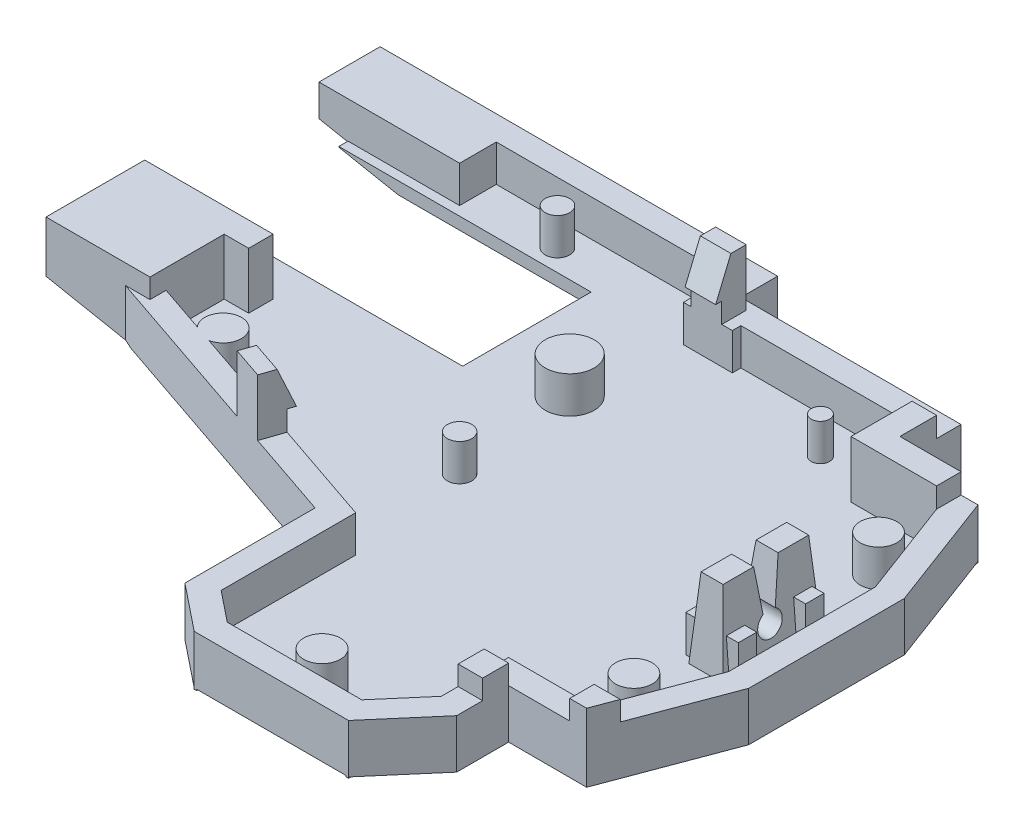
SolidWorks part; units mm, degrees
ref_plane "Front Plane" through (0, 0, 0) normal (0, 0, 1) x (1, 0, 0)
ref_plane "Top Plane" through (0, 0, 0) normal (0, 1, 0) x (1, 0, 0)
ref_plane "Right Plane" through (0, 0, 0) normal (1, 0, 0) x (0, 0, -1)
sketch "Sketch13" plane through (0, 0, 0) normal (0, 1, 0) x (1, 0, 0)
  line L1 (0, 0) -> (50, 0)
  line L2 (0, 0) -> (0, -45)
  line L3 (0, -45) -> (50, -45)
  line L4 (50, 0) -> (50, -45)
  dimension "D1" = 50
extrude "Boss-Extrude4" add sketch "Sketch13" along normal blind 1.6
sketch "Sketch14" plane through (0, 1.6, 0) normal (0, 1, 0) x (1, 0, 0)
  line L1 (50, 0) -> (40, 0)
  line L2 (50, 0) -> (50, -8)
  line L3 (50, -8) -> (40, -8)
  line L4 (40, 0) -> (40, -8)
extrude "Cut-Extrude6" cut sketch "Sketch14" against normal through all
sketch "Sketch15" plane through (0, 1.6, 0) normal (0, 1, 0) x (1, 0, 0)
  line L1 (40, 0) -> (22, 0)
  line L2 (40, 0) -> (40, -3)
  line L3 (40, -3) -> (22, -3)
  line L4 (22, 0) -> (22, -3)
extrude "Cut-Extrude7" cut sketch "Sketch15" against normal through all
sketch "Sketch16" plane through (0, 1.6, 0) normal (0, 1, 0) x (1, 0, 0)
  line L1 (22, -3) -> (26, -3)
  line L2 (22, -3) -> (22, -3.7)
  line L3 (22, -3.7) -> (26, -3.7)
  line L4 (26, -3) -> (26, -3.7)
  dimension "D1" = 0.7
  dimension "D2" = 4
extrude "Cut-Extrude8" cut sketch "Sketch16" against normal through all
sketch "Sketch17" plane through (0, 1.6, 0) normal (0, 1, 0) x (1, 0, 0)
  line L3 (40, -8) -> (50, -8) construction
  line L4 (47, -8) -> (50, -16)
  line L6 (50, -45) -> (50, -8) construction
  line L7 (50, -16) -> (65.8811, -16)
  line L8 (65.8811, -16) -> (65.8811, 17.9573)
  line L9 (65.8811, 17.9573) -> (47, 17.9573)
  line L10 (47, 17.9573) -> (47, -8)
extrude "Cut-Extrude9" cut sketch "Sketch17" against normal through all
sketch "Sketch18" plane through (0, 1.6, 0) normal (0, 1, 0) x (1, 0, 0)
  line L0 (40, -8) -> (40, -36) construction
  line L2 (40, -36) -> (61.1096, -36)
  line L3 (40, -36) -> (40, -58.8405)
  line L4 (40, -58.8405) -> (61.1096, -58.8405)
  line L5 (61.1096, -36) -> (61.1096, -58.8405)
extrude "Cut-Extrude10" cut sketch "Sketch18" against normal through all
sketch "Sketch21" plane through (0, 1.6, 0) normal (0, 1, 0) x (1, 0, 0)
  line L0 (50, -16) -> (27.9365, -16) construction
  line L1 (47, -36) -> (47, -28) construction
  line L2 (50, -36) -> (40, -36) construction
  line L3 (50, -28) -> (47, -36)
  line L4 (50, -36) -> (50, -16) construction
  line L5 (47, -36) -> (47, -49.2976)
  line L6 (47, -49.2976) -> (75.1968, -49.2976)
  line L7 (75.1968, -49.2976) -> (75.1968, -28)
  line L8 (75.1968, -28) -> (50, -28)
extrude "Cut-Extrude11" cut sketch "Sketch21" against normal through all
sketch "Sketch22" plane through (0, 1.6, 0) normal (0, 1, 0) x (1, 0, 0)
  line L0 (0, 0) -> (0, -19.3362) construction
  line L1 (0, 0) -> (0, -45) construction
  line L4 (0, -19.3362) -> (2, -19.3362)
  line L5 (0, -19.3362) -> (0, -22.3362)
  line L6 (0, -22.3362) -> (2, -22.3362)
  line L7 (2, -19.3362) -> (2, -22.3362)
  dimension "D1" = 2
  dimension "D2" = 3
extrude "Cut-Extrude12" cut sketch "Sketch22" against normal through all
sketch "Sketch23" plane through (0, 1.6, 0) normal (0, 1, 0) x (1, 0, 0)
  line L0 (40, -45) -> (23.5, -45) construction
  line L1 (0, -45) -> (40, -45) construction
  line L2 (23.5, -45) -> (23.5, -32)
  line L3 (0, -22.3362) -> (0, -26.3362) construction
  line L4 (0, -22.3362) -> (0, -45) construction
  line L5 (23.5, -32) -> (0, -26.3362)
  line L6 (0, -26.3362) -> (-30.2262, -26.3362)
  line L7 (-30.2262, -26.3362) -> (-30.2262, -63.1883)
  line L8 (-30.2262, -63.1883) -> (23.5, -63.1883)
  line L9 (23.5, -63.1883) -> (23.5, -45)
extrude "Cut-Extrude13" cut sketch "Sketch23" against normal through all
sketch "Sketch24" plane through (0, 1.6, 0) normal (0, 1, 0) x (1, 0, 0)
  line L0 (23.5, -43) -> (7.4911, -43)
  line L1 (23.5, -45) -> (40, -45) construction
  line L2 (7.4911, -43) -> (7.4911, -69.5502)
  line L3 (40, -36) -> (40, -45) construction
  line L4 (37, -45) -> (40, -41.5)
  line L5 (23.5, -45) -> (23.5, -32) construction
  line L6 (26, -45) -> (23.5, -43)
  line L7 (7.4911, -69.5502) -> (44.754, -69.5502)
  line L8 (44.754, -69.5502) -> (44.754, -41.5)
  line L9 (44.754, -41.5) -> (40, -41.5)
  line L10 (37, -45) -> (26, -45)
extrude "Cut-Extrude14" cut sketch "Sketch24" against normal through all
sketch "Sketch25" plane through (0, 1.6, 0) normal (0, 1, 0) x (1, 0, 0)
  line L0 (50, -22) -> (47.6007, -22.0598) construction
  line L1 (50, -28) -> (50, -16) construction
  line L2 (47.6007, -22.0598) -> (47.6007, -18.0598) construction
  line L4 (47.6007, -18.0598) -> (44.8007, -18.0598)
  line L5 (47.6007, -18.0598) -> (47.6007, -26.0598)
  line L6 (47.6007, -26.0598) -> (44.8007, -26.0598)
  line L7 (44.8007, -18.0598) -> (44.8007, -26.0598)
  dimension "D1" = 2.8
  dimension "D2" = 8
extrude "Cut-Extrude15" cut sketch "Sketch25" against normal through all
sketch "Sketch28" plane through (0, 0, 0) normal (0, -1, 0) x (1, 0, 0)
  line L44 (42, 38) -> (42, 42.2398)
  line L45 (42, 42.2398) -> (37.9199, 47)
  line L46 (37.9199, 47) -> (25.2984, 47)
  line L47 (25.2984, 47) -> (21.5, 43.9612)
  line L48 (21.5, 43.9612) -> (21.5, 33.5752)
  line L49 (21.5, 33.5752) -> (-2, 27.9115)
  line L50 (-2, 27.9115) -> (-2, -2)
  line L51 (-2, -2) -> (24, -2)
  line L52 (24, -2) -> (24, 1)
  line L53 (24, 1) -> (42, 1)
  line L54 (42, 1) -> (42, 6)
  line L55 (42, 6) -> (48.386, 6)
  line L56 (48.386, 6) -> (52, 15.6373)
  line L57 (52, 15.6373) -> (52, 28.3627)
  line L58 (52, 28.3627) -> (48.386, 38)
  line L59 (48.386, 38) -> (42, 38)
  line L60 (42, 38) -> (42, 42.2398)
  line L61 (42, 42.2398) -> (37.9199, 47)
  line L62 (37.9199, 47) -> (25.2984, 47)
  line L63 (25.2984, 47) -> (21.5, 43.9612)
  line L64 (21.5, 43.9612) -> (21.5, 33.5752)
  line L65 (21.5, 33.5752) -> (-2, 27.9115)
  line L66 (-2, 27.9115) -> (-2, -2)
  line L67 (-2, -2) -> (24, -2)
  line L68 (24, -2) -> (24, 1)
  line L69 (24, 1) -> (42, 1)
  line L70 (42, 1) -> (42, 6)
  line L71 (42, 6) -> (48.386, 6)
  line L72 (48.386, 6) -> (52, 15.6373)
  line L73 (52, 15.6373) -> (52, 28.3627)
  line L74 (52, 28.3627) -> (48.386, 38)
  line L75 (48.386, 38) -> (42, 38)
  dimension "D1" = 2
extrude "Boss-Extrude6" add sketch "Sketch28" along normal blind 6
sketch "Sketch30" plane through (0, 0, 0) normal (0, 1, 0) x (1, 0, 0)
  line L8 (44.8007, -18.0598) -> (44.8007, -26.0598)
  line L9 (44.8007, -26.0598) -> (47.6007, -26.0598)
  line L10 (47.6007, -26.0598) -> (47.6007, -18.0598)
  line L11 (47.6007, -18.0598) -> (44.8007, -18.0598)
  line L12 (44.8007, -18.0598) -> (44.8007, -26.0598)
  line L13 (44.8007, -26.0598) -> (47.6007, -26.0598)
  line L14 (47.6007, -26.0598) -> (47.6007, -18.0598)
  line L15 (47.6007, -18.0598) -> (44.8007, -18.0598)
  dimension "D1" = 0
extrude "Boss-Extrude7" add sketch "Sketch30" along normal blind 3.5
sketch "Sketch31" plane through (0, 1.6, 0) normal (0, 1, 0) x (1, 0, 0)
  line L44 (37, -45) -> (40, -41.5)
  line L45 (40, -41.5) -> (40, -36)
  line L46 (40, -36) -> (47, -36)
  line L47 (47, -36) -> (50, -28)
  line L48 (50, -28) -> (50, -16)
  line L49 (50, -16) -> (47, -8)
  line L50 (47, -8) -> (40, -8)
  line L51 (40, -8) -> (40, -3)
  line L52 (40, -3) -> (26, -3)
  line L53 (26, -3) -> (26, -3.7)
  line L54 (26, -3.7) -> (22, -3.7)
  line L55 (22, -3.7) -> (22, 0)
  line L56 (22, 0) -> (0, 0)
  line L57 (0, 0) -> (0, -19.3362)
  line L58 (0, -19.3362) -> (2, -19.3362)
  line L59 (2, -19.3362) -> (2, -22.3362)
  line L60 (2, -22.3362) -> (0, -22.3362)
  line L61 (0, -22.3362) -> (0, -26.3362)
  line L62 (0, -26.3362) -> (23.5, -32)
  line L63 (23.5, -32) -> (23.5, -43)
  line L64 (23.5, -43) -> (26, -45)
  line L65 (26, -45) -> (37, -45)
  line L66 (37, -45) -> (40, -41.5)
  line L67 (40, -41.5) -> (40, -36)
  line L68 (40, -36) -> (47, -36)
  line L69 (47, -36) -> (50, -28)
  line L70 (50, -28) -> (50, -16)
  line L71 (50, -16) -> (47, -8)
  line L72 (47, -8) -> (40, -8)
  line L73 (40, -8) -> (40, -3)
  line L74 (40, -3) -> (26, -3)
  line L75 (26, -3) -> (26, -3.7)
  line L76 (26, -3.7) -> (22, -3.7)
  line L77 (22, -3.7) -> (22, 0)
  line L78 (22, 0) -> (0, 0)
  line L79 (0, 0) -> (0, -19.3362)
  line L80 (0, -19.3362) -> (2, -19.3362)
  line L81 (2, -19.3362) -> (2, -22.3362)
  line L82 (2, -22.3362) -> (0, -22.3362)
  line L83 (0, -22.3362) -> (0, -26.3362)
  line L84 (0, -26.3362) -> (23.5, -32)
  line L85 (23.5, -32) -> (23.5, -43)
  line L86 (23.5, -43) -> (26, -45)
  line L87 (26, -45) -> (37, -45)
  dimension "D1" = 0
extrude "Cut-Extrude16" cut sketch "Sketch31" against normal blind 4.6
sketch "Sketch32" plane through (0, 1.6, 0) normal (0, -1, 0) x (1, 0, 0)
  line L8 (47.6007, 18.0598) -> (47.6007, 26.0598)
  line L9 (47.6007, 26.0598) -> (44.8007, 26.0598)
  line L10 (44.8007, 26.0598) -> (44.8007, 18.0598)
  line L11 (44.8007, 18.0598) -> (47.6007, 18.0598)
  line L12 (47.6007, 18.0598) -> (47.6007, 26.0598)
  line L13 (47.6007, 26.0598) -> (44.8007, 26.0598)
  line L14 (44.8007, 26.0598) -> (44.8007, 18.0598)
  line L15 (44.8007, 18.0598) -> (47.6007, 18.0598)
  dimension "D1" = 0
extrude "Boss-Extrude8" add sketch "Sketch32" along normal blind 4.6
sketch "Sketch35" plane through (47.6007, 0, 0) normal (1, 0, 0) x (0, 0, -1)
  line L0 (-22.0598, 3.5) -> (-22.0598, 0) construction
  line L1 (-26.0598, 3.5) -> (-18.0598, 3.5) construction
  line L2 (-22.0598, 3.5) -> (-21.0598, 3.5) construction
  line L3 (-22.0598, 3.5) -> (-23.0598, 3.5) construction
  line L4 (-22.0598, 0) -> (-21.5598, 0)
  line L5 (-21.5598, 0) -> (-21.0598, 3.5)
  line L6 (-22.0598, 0) -> (-22.5598, 0)
  line L7 (-22.5598, 0) -> (-23.0598, 3.5)
  line L8 (-23.0598, 3.5) -> (-23.2577, 4.8851)
  line L9 (-21.0598, 3.5) -> (-21.2977, 5.1651)
  line L10 (-21.2977, 5.1651) -> (-23.2577, 4.8851)
extrude "Cut-Extrude18" cut sketch "Sketch35" against normal blind 4.6
sketch "Sketch37" plane through (47.6007, 0, 0) normal (1, 0, 0) x (0, 0, -1)
  line L0 (-22.0598, 0) -> (-22.0598, -3.4808) construction
  line L1 (-22.5598, 0) -> (-21.5598, 0) construction
  line L2 (-21.5598, 0) -> (-22.0598, -0.866) construction
  circle A0 centre (-22.0598, -0.866) radius 1
extrude "Cut-Extrude19" cut sketch "Sketch37" against normal blind 4.6
sketch "Sketch39" plane through (44.8007, 0, 0) normal (-1, 0, 0) x (0, 0, 1)
  line L0 (26.0598, 3.5) -> (25.5598, 3.5) construction
  line L1 (23.0598, 3.5) -> (26.0598, 3.5) construction
  line L2 (25.5598, 3.5) -> (26.0598, -3)
  line L3 (26.0598, -3) -> (27.9064, -2.858)
  line L4 (27.9064, -2.858) -> (27.4064, 3.642)
  line L5 (27.4064, 3.642) -> (25.5598, 3.5)
  line L6 (18.0598, 3.5) -> (18.5598, 3.5) construction
  line L7 (18.0598, 3.5) -> (21.0598, 3.5) construction
  line L8 (18.5598, 3.5) -> (18.0598, -3)
  line L9 (18.0598, -3) -> (15.9573, -2.8383)
  line L10 (15.9573, -2.8383) -> (16.4557, 3.642)
  line L11 (16.4557, 3.642) -> (18.5598, 3.5)
extrude "Cut-Extrude20" cut sketch "Sketch39" against normal blind 4.6
sketch "Sketch41" plane through (0, 0, 0) normal (0, 0, 1) x (1, 0, 0)
  line L0 (44.8007, 3.5) -> (45.3007, 3.5) construction
  line L1 (44.8007, 3.5) -> (47.6007, 3.5) construction
  line L2 (47.6007, 3.5) -> (47.1007, 3.5) construction
  line L3 (45.3007, 3.5) -> (44.8007, -3)
  line L4 (44.8007, -3) -> (43.415, -2.8934)
  line L5 (43.415, -2.8934) -> (43.9406, 3.9398)
  line L6 (43.9406, 3.9398) -> (45.3007, 3.5)
  line L7 (47.1007, 3.5) -> (47.6007, -3)
  line L8 (47.6007, -3) -> (49.659, -2.8417)
  line L9 (49.659, -2.8417) -> (49.1373, 3.9398)
  line L10 (49.1373, 3.9398) -> (47.1007, 3.5)
extrude "Cut-Extrude21" cut sketch "Sketch41" along normal up to vertex
sketch "Sketch43" plane through (0, 0, 0) normal (0, 1, 0) x (1, 0, 0)
  line L0 (47, -8) -> (50, -16)
  line L1 (50, -16) -> (51.1704, -13.4251)
  line L2 (49.4404, -8.8117) -> (52, -15.6373) construction
  line L3 (46.2007, -6) -> (51.8278, -6) construction
  line L4 (45.0315, -6) -> (47.37, -6) construction
  line L5 (50.6159, -11.9464) -> (47.8466, -4.5615) construction
  line L6 (51.1704, -13.4251) -> (48.386, -6)
  line L7 (48.386, -6) -> (42.8188, -6)
  line L8 (42, -6) -> (43.6375, -6) construction
  line L9 (42.8188, -6) -> (42.8188, -8)
  line L10 (40, -8) -> (43.6375, -8) construction
  line L11 (42.8188, -8) -> (47, -8)
extrude "Boss-Extrude9" add sketch "Sketch43" against normal blind 4.6
sketch "Sketch44" plane through (0, -3, 0) normal (0, 1, 0) x (1, 0, 0)
  line L0 (47.6007, -18.0598) -> (47.6007, -18.5598) construction
  line L1 (47.6007, -18.0598) -> (47.6007, -26.0598) construction
  line L2 (47.6007, -18.5598) -> (48.3507, -18.5598) construction
  line L3 (44.8007, -18.5598) -> (44.0507, -18.5598) construction
  line L4 (44.8007, -26.0598) -> (44.8007, -18.0598) construction
  line L5 (47.6007, -26.0598) -> (47.6007, -25.5598) construction
  line L6 (48.3507, -25.5598) -> (44.0507, -25.5598) construction
  line L7 (48.3507, -18.5598) -> (48.3507, -20.0598)
  line L8 (48.3507, -25.5598) -> (48.3507, -24.0598)
  line L9 (48.3507, -24.0598) -> (44.0507, -24.0598)
  line L10 (44.0507, -24.0598) -> (44.0507, -25.5598)
  line L11 (44.0507, -25.5598) -> (48.3507, -25.5598)
  line L12 (48.3507, -20.0598) -> (44.0507, -20.0598)
  line L13 (44.0507, -20.0598) -> (44.0507, -18.5598)
  line L14 (44.0507, -18.5598) -> (48.3507, -18.5598)
extrude "Boss-Extrude11" add sketch "Sketch44" along normal blind 3
sketch "Sketch45" plane through (0, -3, 0) normal (0, 1, 0) x (1, 0, 0)
  line L0 (50, -22) -> (44, -22) construction
  line L1 (50, -28) -> (50, -16) construction
  line L2 (44, -22) -> (44, -32) construction
  line L3 (44, -32) -> (46.25, -32) construction
  line L4 (44, -22) -> (44, -12) construction
  line L5 (22, -3.7) -> (22, -22) construction
  line L6 (22, -22) -> (22, -21) construction
  line L7 (40, -36) -> (23.5, -36) construction
  line L8 (23.5, -32) -> (23.5, -43) construction
  line L9 (31.75, -45) -> (31.75, -43) construction
  line L10 (26, -45) -> (37, -45) construction
  line L11 (40, -3) -> (40, -6) construction
  line L12 (40, -8) -> (40, -3) construction
  line L13 (40, -6) -> (35.5, -6) construction
  line L14 (22, 0) -> (22, -2) construction
  line L15 (22, 0) -> (0, 0) construction
  line L16 (22, -3.7) -> (22, 0) construction
  line L17 (22, -2) -> (10, -2) construction
  line L18 (0, -24.3362) -> (5, -24.3362) construction
  line L19 (0, -22.3362) -> (0, -26.3362) construction
  circle A0 centre (46.25, -12) radius 1.5
  circle A1 centre (46.25, -32) radius 1.5
  circle A2 centre (22, -22) radius 1
  circle A3 centre (21, -12) radius 1.9996
  circle A4 centre (31.75, -43) radius 1.5033
  circle A5 centre (35.5, -6) radius 0.75
  circle A6 centre (10, -2) radius 1
  circle A7 centre (5, -24.3362) radius 1.5
extrude "Boss-Extrude12" add sketch "Sketch45" along normal blind 3
sketch "Sketch46" plane through (0, 0, 0) normal (0, 1, 0) x (1, 0, 0)
  line L0 (14.1373, -29.7435) -> (16.5677, -30.3292)
  line L1 (16.5677, -30.3292) -> (16.0991, -32.2736)
  line L2 (21.5, -33.5752) -> (-2, -27.9115) construction
  line L3 (16.0991, -32.2736) -> (13.6687, -31.6878)
  line L4 (13.6687, -31.6878) -> (14.1373, -29.7435)
  line L5 (24, -3.7) -> (25.1336, -3.7) construction
  line L6 (22, -3.7) -> (26, -3.7) construction
  line L7 (25.1336, -3.7) -> (22.6336, -3.7)
  line L8 (22.6336, -3.7) -> (22.6336, -1.7)
  line L9 (22.6336, -1.7) -> (25.1336, -1.7)
  line L10 (25.1336, -1.7) -> (25.1336, -3.7)
  line L11 (2, -20.8362) -> (2, -19.9327) construction
  line L12 (2, -22.3362) -> (2, -19.3362) construction
  line L13 (2, -19.9327) -> (2, -21.9327)
  line L14 (2, -21.9327) -> (0, -21.9327)
  line L15 (0, -21.9327) -> (0, -19.9327)
  line L16 (0, -19.9327) -> (2, -19.9327)
  line L17 (23.5, -32) -> (0, -26.3362) construction
  line L18 (16.5677, -30.3292) -> (14.1373, -29.7435) construction
  line L19 (47, -36) -> (48.8727, -36.7022)
  line L20 (52, -28.3627) -> (48.386, -38) construction
  line L21 (48.8727, -36.7022) -> (49.7505, -34.3614)
  line L22 (49.7505, -34.3614) -> (47.8778, -33.6592)
  line L23 (50, -28) -> (47, -36) construction
  line L24 (47.8778, -33.6592) -> (47, -36)
  line L25 (40, -3) -> (40, -8)
  line L26 (26, -3) -> (40, -3) construction
  line L27 (40, -3) -> (40, -8) construction
  line L28 (40, -8) -> (47, -8)
  line L29 (47, -8) -> (47, -6)
  line L30 (42, -6) -> (48.386, -6) construction
  line L31 (47, -6) -> (42, -6)
  line L32 (42, -6) -> (42, -3)
  line L33 (42, -1) -> (42, -6) construction
  line L34 (42, -3) -> (40, -3)
extrude "Boss-Extrude13" add sketch "Sketch46" along normal blind 1.65
sketch "Sketch47" plane through (0, 0, 0) normal (0, 1, 0) x (1, 0, 0)
  line L1 (0, 0) -> (3, 0)
  line L2 (0, 0) -> (0, -3)
  line L3 (0, -3) -> (3, -3)
  line L4 (3, 0) -> (3, -3)
extrude "Boss-Extrude14" add sketch "Sketch47" against normal up to surface (3 mm away) up to face at (10, -3, 3)
sketch "Sketch48" plane through (0, 0, 0) normal (0, 1, 0) x (1, 0, 0)
  line L0 (-2, -27.9115) -> (-2, 2) construction
  line L1 (0, -19.3362) -> (-2, -19.3362)
  line L2 (0, -19.3362) -> (0, -3)
  line L3 (0, -3) -> (-2, -3)
  line L4 (-2, -19.3362) -> (-2, -3)
extrude "Cut-Extrude22" cut sketch "Sketch48" against normal up to surface (3 mm away) up to face at (23.75, -3, 19.4826)
sketch "Sketch49" plane through (-2, 0, 0) normal (-1, 0, 0) x (0, 0, 1)
  line L1 (-2, -6) -> (19.3362, -6)
  line L2 (-2, -6) -> (-2, -3)
  line L3 (-2, -3) -> (19.3362, -3)
  line L4 (19.3362, -6) -> (19.3362, -3)
extrude "Boss-Extrude15" add sketch "Sketch49" along normal blind 13
sketch "Sketch50" plane through (0, -6, 0) normal (0, -1, 0) x (1, 0, 0)
  line L0 (52, 22) -> (52, -11.4177) construction
  line L1 (52, 15.6373) -> (52, 28.3627) construction
  line L2 (24, -2) -> (52, -2) construction
  line L3 (52, 22) -> (52, 58.8348) construction
  line L4 (34.4271, 47) -> (52, 47) construction
  line L5 (37.9199, 47) -> (25.2984, 47) construction
  line L7 (-15, -2) -> (52, -2)
  line L8 (-15, -2) -> (-15, 47)
  line L9 (-15, 47) -> (52, 47)
  line L10 (52, -2) -> (52, 47)
extrude "Boss-Extrude16" add sketch "Sketch50" against normal up to surface (3 mm away) up to face at (19.6296, -3, 17.9784)
sketch "Sketch51" plane through (0, -3, 0) normal (0, 1, 0) x (1, 0, 0)
  line L0 (47.6007, -26.0598) -> (47.6007, -47) construction
  line L1 (52, -47) -> (37.9199, -47) construction
  line L3 (47, -36) -> (52, -36)
  line L4 (47, -36) -> (47, -47)
  line L5 (47, -47) -> (52, -47)
  line L6 (52, -36) -> (52, -47)
extrude "Boss-Extrude17" add sketch "Sketch51" along normal blind 15.6
sketch "Sketch52" plane through (0, 1.65, 0) normal (0, 1, 0) x (1, 0, 0)
  line L8 (47.8778, -33.6592) -> (47, -36)
  line L9 (47, -36) -> (49.136, -36)
  line L10 (49.136, -36) -> (49.7505, -34.3614)
  line L11 (49.7505, -34.3614) -> (47.8778, -33.6592)
  line L12 (47.8778, -33.6592) -> (47, -36)
  line L13 (47, -36) -> (49.136, -36)
  line L14 (49.136, -36) -> (49.7505, -34.3614)
  line L15 (49.7505, -34.3614) -> (47.8778, -33.6592)
  dimension "D1" = 0
extrude "Cut-Extrude23" cut sketch "Sketch52" against normal up to surface (1.65 mm away) up to face at (49.3349, 0, 19.5578)
sketch "Sketch53" plane through (0, 0, 0) normal (0, 1, 0) x (1, 0, 0)
  line L0 (40, -36) -> (40, -41.5) construction
  line L1 (40, -37.9906) -> (42, -37.9906)
  line L2 (40, -37.9906) -> (40, -40.1199)
  line L3 (40, -40.1199) -> (42, -40.1199)
  line L4 (42, -37.9906) -> (42, -40.1199)
  line L5 (42, -38) -> (42, -42.2398) construction
extrude "Boss-Extrude18" add sketch "Sketch53" along normal blind 1.6
sketch "Sketch55" plane through (0, 1.65, 0) normal (0, 1, 0) x (1, 0, 0)
  line L1 (22.6336, -1.7) -> (25.1336, -1.7)
  line L2 (22.6336, -1.7) -> (22.6336, -4.2)
  line L3 (22.6336, -4.2) -> (25.1336, -4.2)
  line L4 (25.1336, -1.7) -> (25.1336, -4.2)
extrude "Boss-Extrude20" add sketch "Sketch55" along normal blind 3
sketch "Sketch56" plane through (25.1336, 0, 0) normal (1, 0, 0) x (0, 0, -1)
  line L0 (-4.2, 1.65) -> (-2.95, 4.65)
  line L1 (-4.2, 4.65) -> (-1.7, 4.65) construction
  line L2 (-2.95, 4.65) -> (-2.95, 7.6873)
  line L3 (-2.95, 7.6873) -> (-6.5972, 7.6873)
  line L4 (-6.5972, 7.6873) -> (-6.5972, 1.6413)
  line L5 (-6.5972, 1.6413) -> (-4.2, 1.65)
extrude "Cut-Extrude24" cut sketch "Sketch56" against normal blind 3
sketch "Sketch58" plane through (0, -3, 0) normal (0, 1, 0) x (1, 0, 0)
  line L0 (3, 0) -> (-15, 0) construction
  line L1 (-15, -47) -> (-15, 2) construction
  line L2 (0, -26.3362) -> (7.3396, -26.3362) construction
  line L3 (-15, -19.3362) -> (-15, -16.4918) construction
  line L4 (3, 0) -> (3, -3.75) construction
  line L5 (3, -3.75) -> (-5.5, -3.75) construction
  line L6 (-5.5, -3.75) -> (14.5, -3.75)
  line L7 (-5.5, -3.75) -> (-5.5, -14.25)
  line L8 (-5.5, -14.25) -> (14.5, -14.25)
  line L9 (14.5, -3.75) -> (14.5, -14.25)
  line L10 (7.3396, 0) -> (7.3396, -26.3362) construction
  line L11 (22, 0) -> (3, 0) construction
  line L12 (26, -45) -> (6.087, -45) construction
  line L13 (6.087, 0) -> (6.087, -45) construction
  line L14 (0, 0) -> (0, -25) construction
  line L15 (0, -22.3362) -> (0, -26.3362) construction
  line L16 (0, -14.25) -> (0, -17.2489) construction
  line L17 (2, -20.8362) -> (2, -17.2489) construction
  line L18 (2, -19.3362) -> (2, -22.3362) construction
  line L19 (0, -17.2489) -> (2, -17.2489)
  line L20 (2, -17.2489) -> (2, -19.2489)
  line L21 (2, -19.2489) -> (0, -19.2489)
  line L22 (0, -19.2489) -> (0, -17.2489)
extrude "Cut-Extrude29" cut sketch "Sketch58" against normal blind 1
sketch "Sketch60" plane through (0, -3, 0) normal (0, 1, 0) x (1, 0, 0)
  line L0 (27.9182, -45) -> (13.2629, -45) construction
  line L1 (26, -45) -> (37, -45) construction
  line L2 (23.5, -32) -> (23.5, -45) construction
  line L3 (0, 0) -> (0, -24) construction
  line L4 (0, -22.3362) -> (0, -26.3362) construction
  line L5 (0, -24) -> (23.5, -32)
  line L6 (23.5, -32) -> (0, -26.3362)
  line L7 (0, -26.3362) -> (23.5, -32) construction
  line L8 (0, -26.3362) -> (0, -24)
extrude "Boss-Extrude21" add sketch "Sketch60" along normal up to surface (3 mm away) up to face at (49.1691, 0, 20)
sketch "Sketch61" plane through (-5.9989, 0, 24.8904) normal (0.2343, 0, -0.9722) x (-0.9722, 0, -0.2343)
  line L8 (-23.2128, 1.65) -> (-23.2128, 0)
  line L9 (-23.2128, 0) -> (-20.7128, 0)
  line L10 (-20.7128, 0) -> (-20.7128, 1.65)
  line L11 (-20.7128, 1.65) -> (-23.2128, 1.65)
  line L12 (-23.2128, 1.65) -> (-23.2128, 0)
  line L13 (-23.2128, 0) -> (-20.7128, 0)
  line L14 (-20.7128, 0) -> (-20.7128, 1.65)
  line L15 (-20.7128, 1.65) -> (-23.2128, 1.65)
  dimension "D1" = 0
extrude "Boss-Extrude22" add sketch "Sketch61" along normal up to surface (0.8848 mm away)
sketch "Sketch62" plane through (0, 0, 0) normal (0, 1, 0) x (1, 0, 0)
  line L0 (0, -24) -> (0, -26) construction
  line L1 (1.9318, -24.6576) -> (-9.2599, -20.8477) construction
  line L2 (3.8635, -25.3152) -> (0, -24) construction
  line L3 (-9.2599, -20.8477) -> (-9.2599, -22.8477) construction
  line L4 (0, -26) -> (-0.5452, -28.2621)
  line L5 (13.6687, -31.6878) -> (-2, -27.9115) construction
  line L6 (-0.5452, -28.2621) -> (-9.9311, -26)
  line L7 (-9.9311, -26) -> (-9.2599, -22.8477)
  line L8 (-9.2599, -22.8477) -> (0, -26)
extrude "Cut-Extrude30" cut sketch "Sketch62" against normal up to surface (3 mm away) up to face at (35.5, -3, 6.75)
sketch "Sketch63" plane through (-6.4675, 0, 26.8348) normal (-0.2343, 0, 0.9722) x (0.9722, 0, 0.2343)
  line L16 (20.7128, 0) -> (6.0919, 0)
  line L17 (6.0919, 0) -> (6.0919, -3)
  line L18 (6.0919, -3) -> (28.7683, -3)
  line L19 (28.7683, -3) -> (28.7683, 0)
  line L20 (28.7683, 0) -> (23.2128, 0)
  line L21 (23.2128, 0) -> (23.2128, 1.65)
  line L22 (23.2128, 1.65) -> (20.7128, 1.65)
  line L23 (20.7128, 1.65) -> (20.7128, 0)
  line L24 (20.7128, 0) -> (6.0919, 0)
  line L25 (6.0919, 0) -> (6.0919, -3)
  line L26 (6.0919, -3) -> (28.7683, -3)
  line L27 (28.7683, -3) -> (28.7683, 0)
  line L28 (28.7683, 0) -> (23.2128, 0)
  line L29 (23.2128, 0) -> (23.2128, 1.65)
  line L30 (23.2128, 1.65) -> (20.7128, 1.65)
  line L31 (20.7128, 1.65) -> (20.7128, 0)
  dimension "D1" = 0
extrude "Cut-Extrude31" cut sketch "Sketch63" against normal up to surface (0.7539 mm away)
sketch "Sketch64" plane through (0, 1.65, 0) normal (0, 1, 0) x (1, 0, 0)
  line L0 (0, -21.9327) -> (0, -22.9624) construction
  line L2 (0, -22.9624) -> (2.5515, -22.9624)
  line L3 (0, -22.9624) -> (0, -18.6516)
  line L4 (0, -18.6516) -> (2.5515, -18.6516)
  line L5 (2.5515, -22.9624) -> (2.5515, -18.6516)
extrude "Cut-Extrude32" cut sketch "Sketch64" against normal up to surface (4.65 mm away) up to face at (18.4683, -3, 21.8358)
sketch "Sketch65" plane through (0, -4, 0) normal (0, 1, 0) x (1, 0, 0)
  line L8 (0, -17.2489) -> (0, -19.2489)
  line L9 (0, -19.2489) -> (2, -19.2489)
  line L10 (2, -19.2489) -> (2, -17.2489)
  line L11 (2, -17.2489) -> (0, -17.2489)
  line L12 (0, -17.2489) -> (0, -19.2489)
  line L13 (0, -19.2489) -> (2, -19.2489)
  line L14 (2, -19.2489) -> (2, -17.2489)
  line L15 (2, -17.2489) -> (0, -17.2489)
  dimension "D1" = 0
extrude "Boss-Extrude23" add sketch "Sketch65" along normal up to surface (4 mm away) up to face at (49.1691, 0, 20)
sketch "Sketch66" plane through (0, 0, 0) normal (0, 1, 0) x (1, 0, 0)
  line L1 (0, -19.2489) -> (2, -19.2489)
  line L2 (0, -19.2489) -> (0, -17.2489)
  line L3 (0, -17.2489) -> (2, -17.2489)
  line L4 (2, -19.2489) -> (2, -17.2489)
extrude "Boss-Extrude24" add sketch "Sketch66" along normal blind 1.6
sketch "Sketch67" plane through (0, 1.6, 0) normal (0, 1, 0) x (1, 0, 0)
  line L0 (0, -19.2489) -> (2.5, -19.2489)
  line L1 (0, -19.2489) -> (0, -17.2489)
  line L2 (0, -17.2489) -> (2.5, -17.2489)
  line L3 (2.5, -17.2489) -> (2.5, -19.2489)
extrude "Boss-Extrude25" add sketch "Sketch67" along normal blind 3
sketch "Sketch68" plane through (0, 0, 17.2489) normal (0, 0, -1) x (-1, 0, 0)
  line L0 (-2.5, 1.6) -> (-1.25, 4.6)
  line L1 (-2.5, 4.6) -> (0, 4.6) construction
  line L2 (-1.25, 4.6) -> (-1.25, 6.7749)
  line L3 (-1.25, 6.7749) -> (-4.4975, 6.7749)
  line L4 (-4.4975, 6.7749) -> (-4.4975, 1.5671)
  line L5 (-4.4975, 1.5671) -> (-2.5, 1.6)
extrude "Cut-Extrude33" cut sketch "Sketch68" against normal blind 3
sketch "Sketch69" plane through (0, 1.65, 0) normal (0, 1, 0) x (1, 0, 0)
  line L0 (14.3446, -28.8833) -> (16.7212, -29.6923) construction
  line L1 (16.7212, -29.6923) -> (18.8289, -30.4098) construction
  line L2 (16.2758, -31.5407) -> (16.8859, -29.7484) construction
  line L3 (16.2758, -31.5407) -> (16.7212, -29.6923) construction
  line L4 (16.2758, -31.5407) -> (13.8992, -30.7316) construction
  line L5 (14.3446, -28.8833) -> (16.8859, -29.7484)
  line L6 (16.8859, -29.7484) -> (16.2758, -31.5407)
  line L7 (16.2758, -31.5407) -> (12.9279, -30.401) construction
  line L8 (14.3446, -28.8833) -> (13.7345, -30.6756)
  line L9 (13.7345, -30.6756) -> (16.2758, -31.5407)
extrude "Boss-Extrude26" add sketch "Sketch69" against normal up to surface (1.65 mm away) up to face at (49.1691, 0, 20)
sketch "Sketch70" plane through (0, 0, 19.2489) normal (0, 0, 1) x (1, 0, 0)
  line L0 (2.5, 1.6) -> (1.25, 4.6) construction
  line L1 (2.5, 1.6) -> (-2.555, 1.6)
  line L2 (2.5, 1.6) -> (2.5, 7.1604)
  line L3 (2.5, 7.1604) -> (-2.555, 7.1604)
  line L4 (-2.555, 1.6) -> (-2.555, 7.1604)
extrude "Cut-Extrude34" cut sketch "Sketch70" against normal blind 3
sketch "Sketch71" plane through (0, 1.65, 0) normal (0, 1, 0) x (1, 0, 0)
  line L0 (16.2758, -31.5407) -> (17.0814, -29.1741)
  line L1 (16.2758, -31.5407) -> (13.7345, -30.6756)
  line L2 (18.2187, -25.945) -> (17.0814, -29.1741) construction
  line L3 (18.2187, -25.945) -> (16.2758, -31.5407) construction
  line L4 (17.0814, -29.1741) -> (11.4228, -27.2093) construction
  line L5 (13.7345, -30.6756) -> (14.5598, -28.2985)
  line L6 (14.5598, -28.2985) -> (17.0814, -29.1741)
extrude "Boss-Extrude27" add sketch "Sketch71" along normal blind 3
sketch "Sketch72" plane through (24.2076, 0, 8.2409) normal (0.9466, 0, 0.3223) x (0.3223, 0, -0.9466)
  line L0 (-22.1129, 1.65) -> (-23.3629, 4.65)
  line L1 (-24.6129, 4.65) -> (-22.1129, 4.65) construction
  line L2 (-23.3629, 4.65) -> (-23.3629, 7.6948)
  line L3 (-23.3629, 7.6948) -> (-20.7348, 7.6948)
  line L4 (-20.7348, 7.6948) -> (-20.7348, 1.65)
  line L5 (-20.7348, 1.65) -> (-22.1129, 1.65)
extrude "Cut-Extrude35" cut sketch "Sketch72" against normal blind 3
sketch "Sketch73" plane through (21.762, 0, 7.5561) normal (-0.9447, 0, -0.328) x (-0.328, 0, 0.9447)
  line L10 (24.4734, 4.65) -> (23.2234, 4.65)
  line L11 (23.2234, 4.65) -> (21.9734, 1.65)
  line L12 (21.9734, 1.65) -> (22.5801, 1.65)
  line L13 (22.5801, 1.65) -> (24.4734, 1.65)
  line L14 (24.4734, 1.65) -> (24.4734, 4.65)
  line L15 (24.4734, 4.65) -> (23.2234, 4.65)
  line L16 (23.2234, 4.65) -> (21.9734, 1.65)
  line L17 (21.9734, 1.65) -> (22.5801, 1.65)
  line L18 (22.5801, 1.65) -> (24.4734, 1.65)
  line L19 (24.4734, 1.65) -> (24.4734, 4.65)
  dimension "D1" = 0
extrude "Boss-Extrude28" add sketch "Sketch73" along normal up to surface (0.0115 mm away)
sketch "Sketch74" plane through (0, -4, 0) normal (0, 1, 0) x (1, 0, 0)
  line L0 (-5.5, -9) -> (14.5, -9) construction
  line L1 (-5.5, -3.75) -> (-5.5, -14.25) construction
  line L2 (14.5, -14.25) -> (14.5, -3.75) construction
  line L3 (-0.25, -6.1692) -> (-0.25, -11.6692) construction
  line L4 (4.5, -6.1692) -> (4.5, -11.6692) construction
  line L5 (-0.25, -6.1692) -> (9.25, -6.1692) construction
  line L6 (9.25, -6.1692) -> (9.25, -11.6692) construction
  line L7 (2.5808, -9) -> (-0.25, -6.1692) construction
  line L8 (6.4192, -6.1692) -> (2.5808, -6.1692)
  line L9 (9.25, -6.1692) -> (6.4192, -9) construction
  line L10 (6.4192, -11.8308) -> (2.5808, -11.8308)
  arc A0 (2.5808, -6.1692) -> (2.5808, -11.8308) centre (2.5808, -9) ccw
  arc A1 (6.4192, -6.1692) -> (6.4192, -11.8308) centre (6.4192, -9) cw
extrude "Cut-Extrude36" cut sketch "Sketch74" against normal blind 3
fillet "Fillet8" radius 1 4 edges at (-0.25, -6, 9) (4.5, -6, 6.1692) (9.25, -6, 9) (4.5, -6, 11.8308)
sketch "Sketch76" plane through (0, -3, 0) normal (0, 1, 0) x (1, 0, 0)
  line L0 (47, -47) -> (-8, -47) construction
  line L1 (25.2984, -47) -> (-15, -47) construction
  line L2 (-15, -47) -> (-15, -32.5)
  line L3 (-15, -47) -> (-15, 2) construction
  line L4 (-15, -32.5) -> (-8, -32.5)
  line L5 (-8, -32.5) -> (-8, -47)
  line L6 (-8, -47) -> (-15, -47)
extrude "Boss-Extrude29" add sketch "Sketch76" along normal blind 14.5
sketch "Sketch79" plane through (21.6663, 0, 7.3758) normal (-0.9466, 0, -0.3223) x (-0.3223, 0, 0.9466)
  line L12 (22.7196, 0) -> (24.6129, 0)
  line L13 (24.6129, 0) -> (24.6129, 4.65)
  line L14 (24.6129, 4.65) -> (23.3629, 4.65)
  line L15 (23.3629, 4.65) -> (22.1128, 1.65)
  line L16 (22.1128, 1.65) -> (22.7196, 1.65)
  line L17 (22.7196, 1.65) -> (22.7196, 0)
  line L18 (22.7196, 0) -> (24.6129, 0)
  line L19 (24.6129, 0) -> (24.6129, 4.65)
  line L20 (24.6129, 4.65) -> (23.3629, 4.65)
  line L21 (23.3629, 4.65) -> (22.1128, 1.65)
  line L22 (22.1128, 1.65) -> (22.7196, 1.65)
  line L23 (22.7196, 1.65) -> (22.7196, 0)
  dimension "D1" = 0
extrude "Boss-Extrude30" add sketch "Sketch79" along normal blind 2
sketch "Sketch80" plane through (24.2076, 0, 8.2409) normal (0.9466, 0, 0.3223) x (0.3223, 0, -0.9466)
  line L12 (-22.1129, 1.65) -> (-23.3629, 4.65)
  line L13 (-23.3629, 4.65) -> (-24.6129, 4.65)
  line L14 (-24.6129, 4.65) -> (-24.6129, 0)
  line L15 (-24.6129, 0) -> (-22.7196, 0)
  line L16 (-22.7196, 0) -> (-22.7196, 1.65)
  line L17 (-22.7196, 1.65) -> (-22.1129, 1.65)
  line L18 (-22.1129, 1.65) -> (-23.3629, 4.65)
  line L19 (-23.3629, 4.65) -> (-24.6129, 4.65)
  line L20 (-24.6129, 4.65) -> (-24.6129, 0)
  line L21 (-24.6129, 0) -> (-22.7196, 0)
  line L22 (-22.7196, 0) -> (-22.7196, 1.65)
  line L23 (-22.7196, 1.65) -> (-22.1129, 1.65)
  dimension "D1" = 0
extrude "Cut-Extrude37" cut sketch "Sketch80" against normal blind 2
sketch "Sketch83" plane through (19.773, 0, 6.7312) normal (-0.9466, 0, -0.3223) x (-0.3223, 0, 0.9466)
  line L12 (22.7196, 1.65) -> (22.7196, 0)
  line L13 (22.7196, 0) -> (24.6129, 0)
  line L14 (24.6129, 0) -> (24.6129, 4.65)
  line L15 (24.6129, 4.65) -> (23.3629, 4.65)
  line L16 (23.3629, 4.65) -> (22.1128, 1.65)
  line L17 (22.1128, 1.65) -> (22.7196, 1.65)
  line L18 (22.7196, 1.65) -> (22.7196, 0)
  line L19 (22.7196, 0) -> (24.6129, 0)
  line L20 (24.6129, 0) -> (24.6129, 4.65)
  line L21 (24.6129, 4.65) -> (23.3629, 4.65)
  line L22 (23.3629, 4.65) -> (22.1128, 1.65)
  line L23 (22.1128, 1.65) -> (22.7196, 1.65)
  dimension "D1" = 0
extrude "Boss-Extrude31" add sketch "Sketch83" against normal up to surface (2.6845 mm away) up to face at (14.7873, 2.1, 29.7071)
sketch "Sketch85" plane through (0, -3, 0) normal (0, 1, 0) x (1, 0, 0)
  line L1 (-8, -32.5) -> (22.5662, -32.5)
  line L2 (-8, -32.5) -> (-8, -34.2252)
  line L3 (-8, -34.2252) -> (22.5662, -34.2252)
  line L4 (22.5662, -32.5) -> (22.5662, -34.2252)
extrude "Boss-Extrude33" add sketch "Sketch85" along normal up to surface (3 mm away) up to face at (49.1691, 0, 20)
sketch "Sketch86" plane through (0, -3, 0) normal (0, 1, 0) x (1, 0, 0)
  line L10 (21.5, -43.9612) -> (21.5, -34.2252)
  line L11 (21.5, -34.2252) -> (-8, -34.2252)
  line L12 (-8, -34.2252) -> (-8, -47)
  line L13 (-8, -47) -> (25.2984, -47)
  line L14 (25.2984, -47) -> (21.5, -43.9612)
  line L15 (21.5, -43.9612) -> (21.5, -34.2252)
  line L16 (21.5, -34.2252) -> (-8, -34.2252)
  line L17 (-8, -34.2252) -> (-8, -47)
  line L18 (-8, -47) -> (25.2984, -47)
  line L19 (25.2984, -47) -> (21.5, -43.9612)
  dimension "D1" = 0
extrude "Boss-Extrude34" add sketch "Sketch86" along normal up to surface (3 mm away) up to face at (49.1691, 0, 20)
sketch "Sketch87" plane through (0, -3, 0) normal (0, 1, 0) x (1, 0, 0)
  line L10 (37.9199, -47) -> (47, -47)
  line L11 (47, -47) -> (47, -38)
  line L12 (47, -38) -> (42, -38)
  line L13 (42, -38) -> (42, -42.2398)
  line L14 (42, -42.2398) -> (37.9199, -47)
  line L15 (37.9199, -47) -> (47, -47)
  line L16 (47, -47) -> (47, -38)
  line L17 (47, -38) -> (42, -38)
  line L18 (42, -38) -> (42, -42.2398)
  line L19 (42, -42.2398) -> (37.9199, -47)
  dimension "D1" = 0
extrude "Boss-Extrude35" add sketch "Sketch87" along normal up to surface (3 mm away) up to face at (49.1691, 0, 20)
sketch "Sketch88" plane through (0, 0, 0) normal (0, 1, 0) x (1, 0, 0)
  line L1 (-8, -47) -> (19.0938, -47)
  line L2 (-8, -47) -> (-8, -32.5)
  line L3 (-8, -32.5) -> (19.0938, -32.5)
  line L4 (19.0938, -47) -> (19.0938, -32.5)
extrude "Boss-Extrude36" add sketch "Sketch88" along normal blind 1.6
sketch "Sketch90" plane through (0, 11.5, 0) normal (0, 1, 0) x (1, 0, 0)
  line L8 (-15, -47) -> (-8, -47)
  line L9 (-8, -47) -> (-8, -32.5)
  line L10 (-8, -32.5) -> (-15, -32.5)
  line L11 (-15, -32.5) -> (-15, -47)
  line L12 (-15, -47) -> (-8, -47)
  line L13 (-8, -47) -> (-8, -32.5)
  line L14 (-8, -32.5) -> (-15, -32.5)
  line L15 (-15, -32.5) -> (-15, -47)
  dimension "D1" = 0
extrude "Boss-Extrude37" add sketch "Sketch90" along normal blind 1.6
sketch "Sketch93" plane through (0, 12.6, 0) normal (0, 1, 0) x (1, 0, 0)
  line L1 (47, -47) -> (52, -47)
  line L2 (47, -47) -> (47, -36)
  line L3 (47, -36) -> (52, -36)
  line L4 (52, -47) -> (52, -36)
extrude "Boss-Extrude38" add sketch "Sketch93" along normal blind 0.5
sketch "Sketch94" plane through (0, -3, 0) normal (0, 1, 0) x (1, 0, 0)
  line L0 (19.0938, -32.5) -> (-15, -32.5) construction
  line L1 (1.1186, -32.5) -> (9.7243, -32.5)
  line L2 (1.1186, -32.5) -> (1.1186, -30.5)
  line L3 (1.1186, -30.5) -> (9.7243, -30.5)
  line L4 (9.7243, -32.5) -> (9.7243, -30.5)
  dimension "D1" = 2
extrude "Boss-Extrude39" add sketch "Sketch94" along normal blind 15.6
sketch "Sketch96" plane through (0, 12.6, 0) normal (0, 1, 0) x (1, 0, 0)
  line L8 (1.1186, -30.5) -> (1.1186, -32.5)
  line L9 (1.1186, -32.5) -> (9.7243, -32.5)
  line L10 (9.7243, -32.5) -> (9.7243, -30.5)
  line L11 (9.7243, -30.5) -> (1.1186, -30.5)
  line L12 (1.1186, -30.5) -> (1.1186, -32.5)
  line L13 (1.1186, -32.5) -> (9.7243, -32.5)
  line L14 (9.7243, -32.5) -> (9.7243, -30.5)
  line L15 (9.7243, -30.5) -> (1.1186, -30.5)
  dimension "D1" = 0
extrude "Boss-Extrude40" add sketch "Sketch96" along normal blind 0.5
sketch "Sketch97" plane through (0, -6, 0) normal (0, -1, 0) x (1, 0, 0)
  line L1 (-15, 47) -> (-17, 47)
  line L2 (-15, 47) -> (-15, -2)
  line L3 (-15, -2) -> (-17, -2)
  line L4 (-17, 47) -> (-17, -2)
  dimension "D1" = 2
extrude "Boss-Extrude41" add sketch "Sketch97" against normal up to surface (19.1 mm away) up to face at (-11.5, 13.1, 39.75)
sketch "Sketch98" plane through (0, -6, 0) normal (0, -1, 0) x (1, 0, 0)
  line L1 (-17, 47) -> (52, 47)
  line L2 (-17, 47) -> (-17, 49)
  line L3 (-17, 49) -> (52, 49)
  line L4 (52, 47) -> (52, 49)
  dimension "D1" = 2
extrude "Boss-Extrude42" add sketch "Sketch98" against normal up to surface (19.1 mm away) up to face at (-12.75, 13.1, 22.9583)
sketch "Sketch99" plane through (0, 0, 19.3362) normal (0, 0, -1) x (-1, 0, 0)
  line L8 (2, 0) -> (0, 0)
  line L9 (0, 0) -> (0, -3)
  line L10 (0, -3) -> (2, -3)
  line L11 (2, -3) -> (2, 0)
  line L12 (2, 0) -> (0, 0)
  line L13 (0, 0) -> (0, -3)
  line L14 (0, -3) -> (2, -3)
  line L15 (2, -3) -> (2, 0)
  dimension "D1" = 0
extrude "Boss-Extrude43" add sketch "Sketch99" along normal up to surface (2.0874 mm away) up to face at (0.75, -0.125, 17.2489)
sketch "Sketch100" plane through (0, -6, 0) normal (0, -1, 0) x (1, 0, 0)
  line L1 (52, 49) -> (54, 49)
  line L2 (52, 49) -> (52, -2)
  line L3 (52, -2) -> (54, -2)
  line L4 (54, 49) -> (54, -2)
  dimension "D1" = 2
extrude "Boss-Extrude45" add sketch "Sketch100" against normal up to surface (19.1 mm away) up to face at (9.4, 13.1, 30.95)
sketch "Sketch101" plane through (0, -6, 0) normal (0, -1, 0) x (1, 0, 0)
  line L1 (54, -2) -> (-17, -2)
  line L2 (54, -2) -> (54, -4)
  line L3 (54, -4) -> (-17, -4)
  line L4 (-17, -2) -> (-17, -4)
  dimension "D1" = 2
extrude "Boss-Extrude46" add sketch "Sketch101" against normal up to surface (19.1 mm away) up to face at (17.0417, 13.1, 27.0417)
sketch "Sketch102" plane through (0, -3, 0) normal (0, 1, 0) x (1, 0, 0)
  line L0 (24, 2) -> (52, 2) construction
  line L1 (52, 2) -> (52, -15.6373) construction
  line L2 (52, 0) -> (50, 0) construction
  line L3 (50, 2) -> (50, 2.8367)
  line L4 (50, 2.8367) -> (52.9285, 2.8367)
  line L5 (52.9285, 2.8367) -> (52.9285, 0)
  line L6 (52.9285, 0) -> (52, 0)
  arc A0 (52, 0) -> (50, 2) centre (50, 0) ccw
extrude "Boss-Extrude47" add sketch "Sketch102" along normal up to surface (16.1 mm away)
sketch "Sketch103" plane through (0, -3, 0) normal (0, 1, 0) x (1, 0, 0)
  line L0 (-15, 2) -> (-13, 2) construction
  line L1 (-15, 2) -> (-2, 2) construction
  line L2 (-13, 2) -> (-13, 0) construction
  line L3 (-15, -32.5) -> (-15, 2) construction
  line L4 (-13, 2) -> (-13, 3.3193)
  line L5 (-13, 3.3193) -> (-16.3151, 3.3193)
  line L6 (-16.3151, 3.3193) -> (-16.3151, 0)
  line L7 (-16.3151, 0) -> (-15, 0)
  arc A0 (-13, 2) -> (-15, 0) centre (-13, 0) ccw
extrude "Boss-Extrude48" add sketch "Sketch103" along normal up to surface (16.1 mm away)
fillet "Fillet9" radius 2 8 edges at (18.5, -6, 49) (54, -6, 22.5) (18.5, -6, -4) (-17, -6, 22.5) (-17, 3.55, 49) (54, 3.55, 49) (54, 3.55, -4) (-17, 3.55, -4)
sketch "Sketch105" plane through (0, 13.1, 0) normal (0, 1, 0) x (1, 0, 0)
  line L8 (-16, 2) -> (-16, -47)
  line L9 (-15, -48) -> (52, -48)
  line L10 (53, -47) -> (53, 2)
  line L11 (52, 3) -> (-15, 3)
  line L12 (-16, 2) -> (-16, -47)
  line L13 (-15, -48) -> (52, -48)
  line L14 (53, -47) -> (53, 2)
  line L15 (52, 3) -> (-15, 3)
  arc A8 (-16, -47) -> (-15, -48) centre (-15, -47) ccw
  arc A9 (52, -48) -> (53, -47) centre (52, -47) ccw
  arc A10 (53, 2) -> (52, 3) centre (52, 2) ccw
  arc A11 (-15, 3) -> (-16, 2) centre (-15, 2) ccw
  arc A12 (-16, -47) -> (-15, -48) centre (-15, -47) ccw
  arc A13 (52, -48) -> (53, -47) centre (52, -47) ccw
  arc A14 (53, 2) -> (52, 3) centre (52, 2) ccw
  arc A15 (-15, 3) -> (-16, 2) centre (-15, 2) ccw
  dimension "D1" = 1
extrude "Cut-Extrude38" cut sketch "Sketch105" against normal blind 3 flip side to cut
sketch "Sketch106" plane through (0, -6, 0) normal (0, -1, 0) x (1, 0, 0)
  line L92 (-2, -2) -> (24, -2)
  line L93 (24, -2) -> (24, 1)
  line L94 (24, 1) -> (42, 1)
  line L95 (42, 1) -> (42, 6)
  line L96 (42, 6) -> (48.386, 6)
  line L97 (48.386, 6) -> (52, 15.6373)
  line L98 (52, 15.6373) -> (52, 28.3627)
  line L99 (52, 28.3627) -> (49.136, 36)
  line L100 (42, 40.81) -> (42, 43.4756) construction
  line L102 (40, 40.81) -> (42, 40.81) construction
  line L103 (40, 40.1199) -> (40, 41.5) construction
  line L104 (38.5, 43.25) -> (40.0185, 44.5516) construction
  line L105 (40, 41.5) -> (37, 45) construction
  line L106 (31.5, 45) -> (31.5, 47) construction
  line L107 (26, 45) -> (37, 45) construction
  line L108 (21.5, 33.3191) -> (-2, 25.3191)
  line L110 (-2, 25.3191) -> (-2, 17.2489)
  line L112 (21.5, 33.3191) -> (21.5, 43.9612)
  line L113 (49.136, 36) -> (48.386, 38)
  line L114 (48.386, 38) -> (42, 37.9906)
  line L115 (42, 42.2398) -> (37.9199, 47) construction
  line L116 (-8, 47) -> (47, 47) construction
  line L118 (23.5006, 45.5617) -> (21.5, 43.9612) construction
  line L119 (21.5, 38.4892) -> (21.5, 43.9612) construction
  line L120 (21.5, 43.9612) -> (25.2984, 47)
  line L121 (25.2984, 47) -> (37.9199, 47)
  line L122 (37.9199, 47) -> (42, 42.2398)
  line L123 (42, 42.2398) -> (42, 37.9906)
  line L124 (-2, 17.2489) -> (-8.3721, 17.2489)
  line L125 (-2, 3) -> (-2, -2)
  line L126 (-8.3721, 17.2489) -> (-8.3721, 3)
  line L127 (-8.3721, 3) -> (-2, 3)
  line L129 (56.2206, 50.8933) -> (-20.8354, 50.8933)
  line L130 (56.2206, 50.8933) -> (56.2206, -7.6303)
  line L131 (56.2206, -7.6303) -> (-20.8354, -7.6303)
  line L132 (-20.8354, 50.8933) -> (-20.8354, -7.6303)
extrude "Cut-Extrude39" cut sketch "Sketch106" against normal through all
sketch "Sketch107" plane through (0, 13.1, 0) normal (0, 1, 0) x (1, 0, 0)
  line L1 (51.4721, -35.1845) -> (38.0965, -35.1845)
  line L2 (51.4721, -35.1845) -> (51.4721, -41.3641)
  line L3 (51.4721, -41.3641) -> (38.0965, -41.3641)
  line L4 (38.0965, -35.1845) -> (38.0965, -41.3641)
extrude "Cut-Extrude40" cut sketch "Sketch107" against normal up to surface (11.5 mm away) up to face at (41, 1.6, 39.0552)
sketch "Sketch111" plane through (0, -4, 0) normal (0, 1, 0) x (1, 0, 0)
  circle A0 centre (2.5808, -9) radius 2.8308
sketch "Sketch113" plane through (0, -3, 0) normal (0, 1, 0) x (1, 0, 0)
  line L0 (-6.1286, -3) -> (-6.1286, -14.8614)
  line L1 (-2, -3) -> (-8.3721, -3) construction
  line L2 (-6.1286, -14.8614) -> (-2, -14.8614)
  line L3 (-2, -14.8614) -> (-2, -17.2489)
  line L4 (-2, -17.2489) -> (-9.2465, -26.4524)
  line L5 (-9.2465, -26.4524) -> (-13.8144, -0.6572)
  line L6 (-13.8144, -0.6572) -> (-2.9741, 6.6898)
  line L7 (-2.9741, 6.6898) -> (-3.5377, 5.9741)
  line L8 (-3.5377, 5.9741) -> (-6.1286, -3)
extrude "Cut-Extrude41" cut sketch "Sketch113" against normal through all
sketch "Sketch114" plane through (0, -6, 0) normal (0, -1, 0) x (1, 0, 0)
  line L1 (-8.5229, -3.0253) -> (57.814, -3.0253)
  line L2 (-8.5229, -3.0253) -> (-8.5229, 48.6433)
  line L3 (-8.5229, 48.6433) -> (57.814, 48.6433)
  line L4 (57.814, -3.0253) -> (57.814, 48.6433)
extrude "Cut-Extrude42" cut sketch "Sketch114" against normal up to surface (2 mm away) up to face at (4.5, -4, 9)
sketch "Sketch115" plane through (-2, 0, 0) normal (-1, 0, 0) x (0, 0, 1)
  line L12 (14.8614, -3) -> (14.8614, -4)
  line L13 (14.8614, -4) -> (25.3191, -4)
  line L14 (25.3191, -4) -> (25.3191, 0)
  line L15 (25.3191, 0) -> (17.2489, 0)
  line L16 (17.2489, 0) -> (17.2489, -3)
  line L17 (17.2489, -3) -> (14.8614, -3)
  line L18 (14.8614, -3) -> (14.8614, -4)
  line L19 (14.8614, -4) -> (25.3191, -4)
  line L20 (25.3191, -4) -> (25.3191, 0)
  line L21 (25.3191, 0) -> (17.2489, 0)
  line L22 (17.2489, 0) -> (17.2489, -3)
  line L23 (17.2489, -3) -> (14.8614, -3)
  line L28 (-2, 0) -> (-2, -4)
  line L29 (-2, -4) -> (3, -4)
  line L30 (3, -4) -> (3, -3)
  line L31 (3, -3) -> (3, 0)
  line L32 (3, 0) -> (-2, 0)
  line L33 (-2, 0) -> (-2, -4)
  line L34 (-2, -4) -> (3, -4)
  line L35 (3, -4) -> (3, -3)
  line L36 (3, -3) -> (3, 0)
  line L37 (3, 0) -> (-2, 0)
  dimension "D1" = 0
  dimension "D2" = 0
extrude "Boss-Extrude49" add sketch "Sketch115" along normal blind 6.5
sketch "Sketch116" plane through (0, -3, 0) normal (0, 1, 0) x (1, 0, 0)
  line L0 (-6.1286, -14.8614) -> (-6.1286, -3) construction
  line L1 (-5.5, -3.75) -> (-6.1286, -3.75)
  line L2 (-5.5, -3.75) -> (-5.5, -14.25)
  line L3 (-5.5, -14.25) -> (-6.1286, -14.25)
  line L4 (-6.1286, -3.75) -> (-6.1286, -14.25)
extrude "Cut-Extrude43" cut sketch "Sketch116" against normal blind 6.5
sketch "Sketch117" plane through (0, 0, 0) normal (0, 1, 0) x (1, 0, 0)
  line L1 (-8.5, -25.3191) -> (0, -25.3191)
  line L2 (-8.5, -25.3191) -> (-8.5, -17.2489)
  line L3 (-8.5, -17.2489) -> (0, -17.2489)
  line L4 (0, -25.3191) -> (0, -17.2489)
extrude "Boss-Extrude50" add sketch "Sketch117" along normal up to surface (1.6 mm away) up to face at (0.5, 1.6, 18.4989)
sketch "Sketch118" plane through (0, -4, 0) normal (0, -1, 0) x (1, 0, 0)
  line L0 (-6.1286, 14.25) -> (-6.6286, 14.25)
  line L1 (-6.6286, 14.25) -> (-6.6286, 3.6453)
sketch "Sketch119" plane through (0, 0, 25.3191) normal (0, 0, 1) x (1, 0, 0)
  line L0 (-8.5, -2.6) -> (-1.2976, -4) construction
  line L1 (-8.5, -4) -> (-8.5, 1.6) construction
  line L2 (5.4117, -4) -> (-0.25, -4) construction
  dimension "D1" = 1.4
  dimension "D2" = 7.2024
sketch "Sketch120" plane through (-8.5, 0, 0) normal (-1, 0, 0) x (0, 0, 1)
  line L0 (25.3191, -2.6) -> (-2, -2.6) construction
  line L1 (-2, 0) -> (-2, -4) construction
ref_plane "Plane1" through (-0.7965, -4.0974, 0) normal (0.1908, 0.9816, 0) x (0.9816, -0.1908, 0)
sketch "Sketch121" plane through (-0.7965, -4.0974, 0) normal (0.1908, 0.9816, 0) x (0.9816, -0.1908, 0)
  line L1 (19.9362, -78.5281) -> (-22.0114, -78.5281)
  line L2 (19.9362, -78.5281) -> (19.9362, 26.0108)
  line L3 (19.9362, 26.0108) -> (-22.0114, 26.0108)
  line L4 (-22.0114, -78.5281) -> (-22.0114, 26.0108)
  line L5 (19.9362, -78.5281) -> (-22.0114, 26.0108) construction
  line L6 (19.9362, 26.0108) -> (-22.0114, -78.5281) construction
  point P0 (-1.0376, -26.2587)
extrude "Cut-Extrude44" cut sketch "Sketch121" against normal through all
sketch "Sketch122" plane through (0, -4, 0) normal (0, -1, 0) x (1, 0, 0)
  line L1 (42, 1) -> (41.8, 1)
  line L2 (42, 1) -> (42, 1.2)
  line L3 (42, 1.2) -> (41.8, 1.2)
  line L4 (41.8, 1) -> (41.8, 1.2)
  dimension "D1" = 0.2
sketch "Sketch123" plane through (0, -4, 0) normal (0, -1, 0) x (1, 0, 0)
  line L1 (48.386, 6) -> (48.186, 6)
  line L2 (48.386, 6) -> (48.386, 6.2)
  line L3 (48.386, 6.2) -> (48.186, 6.2)
  line L4 (48.186, 6) -> (48.186, 6.2)
  dimension "D1" = 0.2
sketch "Sketch124" plane through (0, -4, 0) normal (0, -1, 0) x (1, 0, 0)
  line L1 (25.2984, 47) -> (25.4984, 47)
  line L2 (25.2984, 47) -> (25.2984, 46.8)
  line L3 (25.2984, 46.8) -> (25.4984, 46.8)
  line L4 (25.4984, 47) -> (25.4984, 46.8)
  dimension "D1" = 0.2
sketch "Sketch125" plane through (0, -4, 0) normal (0, -1, 0) x (1, 0, 0)
  line L1 (37.9199, 47) -> (37.7199, 47)
  line L2 (37.9199, 47) -> (37.9199, 46.8)
  line L3 (37.9199, 46.8) -> (37.7199, 46.8)
  line L4 (37.7199, 47) -> (37.7199, 46.8)
  dimension "D1" = 0.2
extrude "Boss-Extrude51" add sketch "Sketch122" along normal blind 0.1 contours L4 L3 L2 L1
extrude "Boss-Extrude52" add sketch "Sketch123" along normal blind 0.1 contours L3 L4 L1 L2
extrude "Boss-Extrude53" add sketch "Sketch124" along normal blind 0.1 contours L3 L4 L1 L2
extrude "Boss-Extrude54" add sketch "Sketch125" along normal blind 0.1 contours L3 L4 L1 L2
sketch "Sketch126" plane through (-0.7965, -4.0974, 0) normal (-0.1908, -0.9816, 0) x (0.9816, -0.1908, 0)
  line L0 (3.2966, 9) -> (-5.7436, 9)
  line L1 (-5.7436, 14.25) -> (-5.7436, 3.6453) construction
